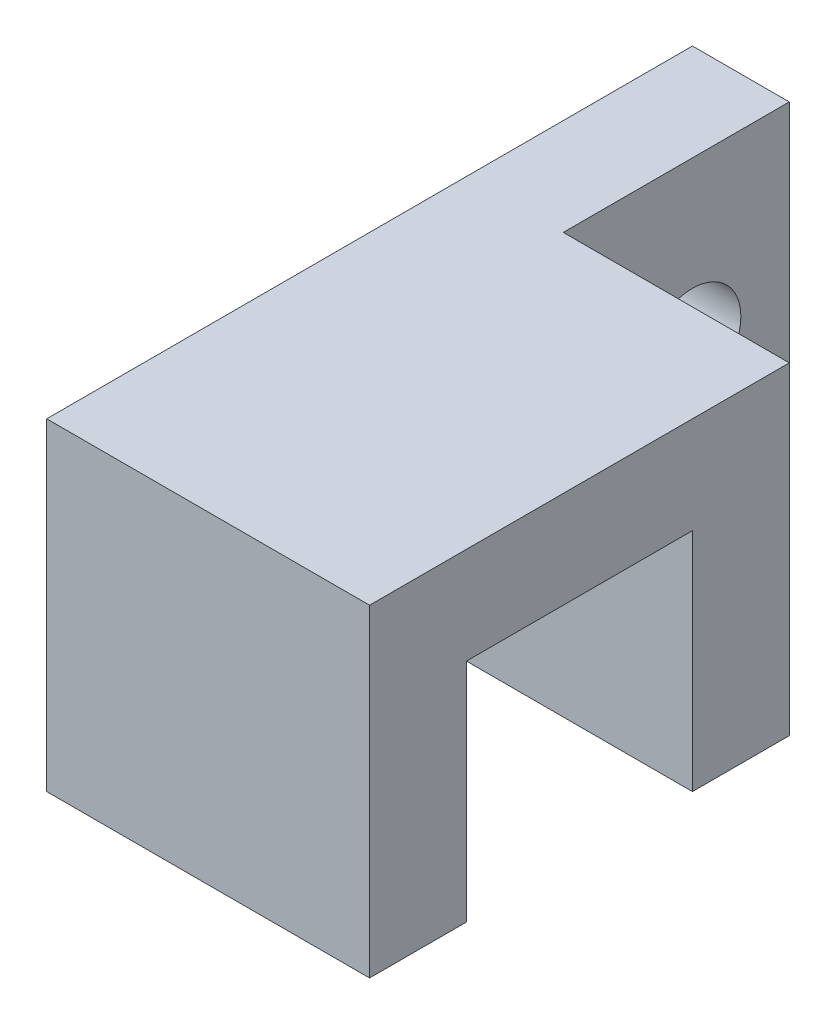
SolidWorks part; units mm, degrees
ref_plane "Front Plane" through (0, 0, 0) normal (0, 0, 1) x (1, 0, 0)
ref_plane "Top Plane" through (0, 0, 0) normal (0, 1, 0) x (1, 0, 0)
ref_plane "Right Plane" through (0, 0, 0) normal (1, 0, 0) x (0, 0, -1)
sketch "Sketch3" plane through (0, 0, 0) normal (0, 1, 0) x (1, 0, 0)
  line L0 (0, 0) -> (63.5, 0)
  line L1 (63.5, 0) -> (63.5, 19.05)
  line L2 (63.5, 19.05) -> (19.05, 19.05)
  line L3 (19.05, 19.05) -> (19.05, 63.5)
  line L4 (19.05, 63.5) -> (0, 63.5)
  line L5 (0, 63.5) -> (0, 0)
  point P6 (0, 0)
  dimension "D1" = 63.5
  dimension "D2" = 19.05
  dimension "D3" = 63.5
  dimension "D4" = 19.05
extrude "Boss-Extrude1" add sketch "Sketch3" along normal blind 63.5
sketch "Sketch5" plane through (63.5, 0, 0) normal (1, 0, 0) x (0, 0, -1)
  line L0 (0, 63.5) -> (-63.5, 63.5)
  line L1 (-63.5, 63.5) -> (-63.5, 0)
  line L2 (-63.5, 0) -> (-44.45, 0)
  line L3 (-44.45, 0) -> (-44.45, 44.45)
  line L4 (-44.45, 44.45) -> (0, 44.45)
  line L5 (0, 63.5) -> (0, 0) construction
  line L6 (0, 44.45) -> (0, 63.5)
  dimension "D1" = 63.5
  dimension "D2" = 63.5
  dimension "D3" = 19.05
  dimension "D4" = 19.05
extrude "Boss-Extrude2" add sketch "Sketch5" against normal blind 63.5
sketch "Sketch6" plane through (19.05, 0, 0) normal (1, 0, 0) x (0, 0, -1)
  line L0 (19.05, 63.5) -> (63.5, 63.5) construction
  line L1 (63.5, 63.5) -> (63.5, 0) construction
  circle A0 centre (44.45, 31.75) radius 9.525
  dimension "D3" = 19.05
  dimension "D1" = 31.75
  dimension "D2" = 19.05
extrude "Cut-Extrude1" cut sketch "Sketch6" against normal through all
